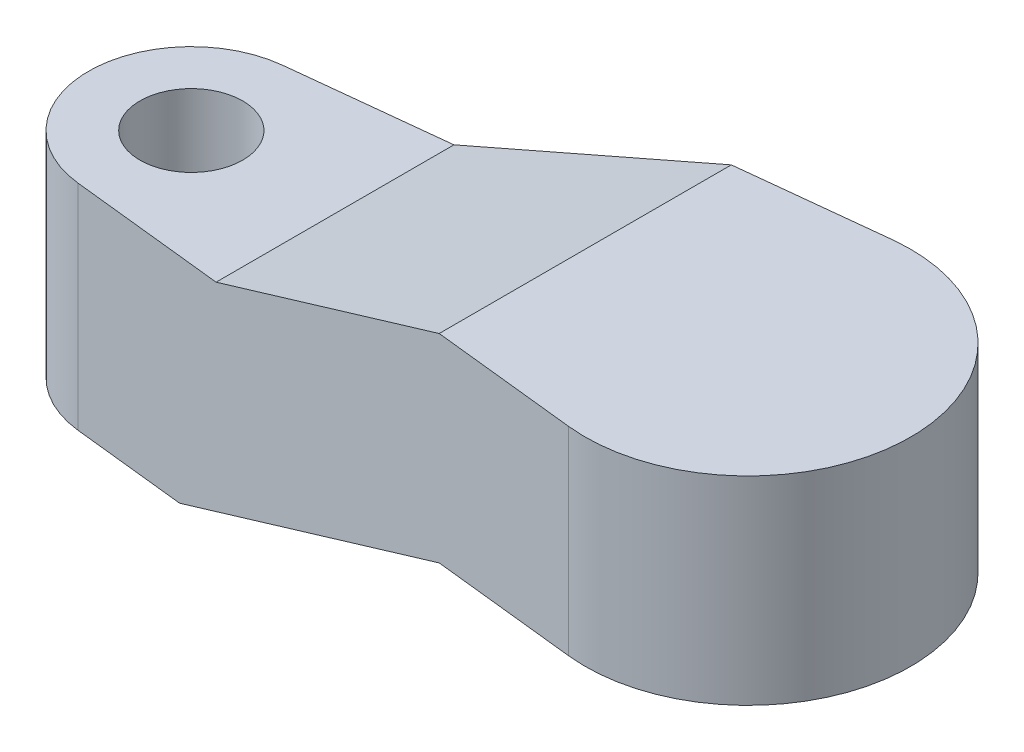
SolidWorks part; units mm, degrees
ref_plane "Front Plane" through (0, 0, 0) normal (0, 0, 1) x (1, 0, 0)
ref_plane "Top Plane" through (0, 0, 0) normal (0, 1, 0) x (1, 0, 0)
ref_plane "Right Plane" through (0, 0, 0) normal (1, 0, 0) x (0, 0, -1)
sketch "Sketch1" plane through (0, 0, 0) normal (0, 1, 0) x (1, 0, 0)
  line L0 (-16.5731, 2.9826) -> (-0.5115, 4.7224)
  line L1 (-16.5731, -2.9826) -> (-0.5115, -4.7224)
  arc A0 (-16.5731, 2.9826) -> (-16.5731, -2.9826) centre (-16.25, 0) ccw
  arc A1 (-0.5115, 4.7224) -> (-0.5115, -4.7224) centre (0, 0) cw
  point P8 (4.75, 0)
  point P9 (-19.25, 0)
  dimension "D1" = 3
  dimension "D2" = 4.75
  dimension "D3" = 24
extrude "Boss-Extrude1" add sketch "Sketch1" along normal blind 9 contours L0 A1 L1 A0
sketch "Sketch2" plane through (0, 0, 0) normal (0, 0, 1) x (1, 0, 0)
  line L0 (-4.75, 9) -> (-12.0547, 6.25)
  line L1 (-16.5731, 9) -> (-0.5115, 9) construction
  line L2 (-12.0547, 6.25) -> (-19.25, 6.25)
  line L3 (-19.25, 9) -> (-19.25, 0) construction
  line L4 (-19.25, 6.25) -> (-19.25, 9)
  line L5 (-16.5731, 9) -> (-19.25, 9) construction
  line L6 (-19.25, 9) -> (-4.75, 9)
  line L7 (-13.25, 0) -> (-4.75, 3.2)
  line L8 (-16.5731, 0) -> (-0.5115, 0) construction
  line L9 (-4.75, 3.2) -> (4.75, 3.2)
  line L10 (4.75, 0) -> (4.75, 9) construction
  line L11 (4.75, 3.2) -> (4.75, 0)
  line L12 (4.75, 0) -> (-13.25, 0)
  dimension "D1" = 5.8
  dimension "D2" = 6.25
  dimension "D3" = 9.5
  dimension "D4" = 6
extrude "Cut-Extrude1" cut sketch "Sketch2" against normal through all both and the other way through all
sketch "Sketch3" plane through (0, 3.2, 0) normal (0, -1, 0) x (1, 0, 0)
  circle A0 centre (0, 0) radius 2
  dimension "D1" = 4
extrude "Cut-Extrude2" cut sketch "Sketch3" against normal blind 2
sketch "Sketch4" plane through (0, 0, 0) normal (0, -1, 0) x (1, 0, 0)
  circle A0 centre (-16.25, 0) radius 1.5
  arc A1 (-16.5731, 2.9826) -> (-16.5731, -2.9826) centre (-16.25, 0) ccw construction
  dimension "D1" = 3
extrude "Cut-Extrude3" cut sketch "Sketch4" against normal through all
